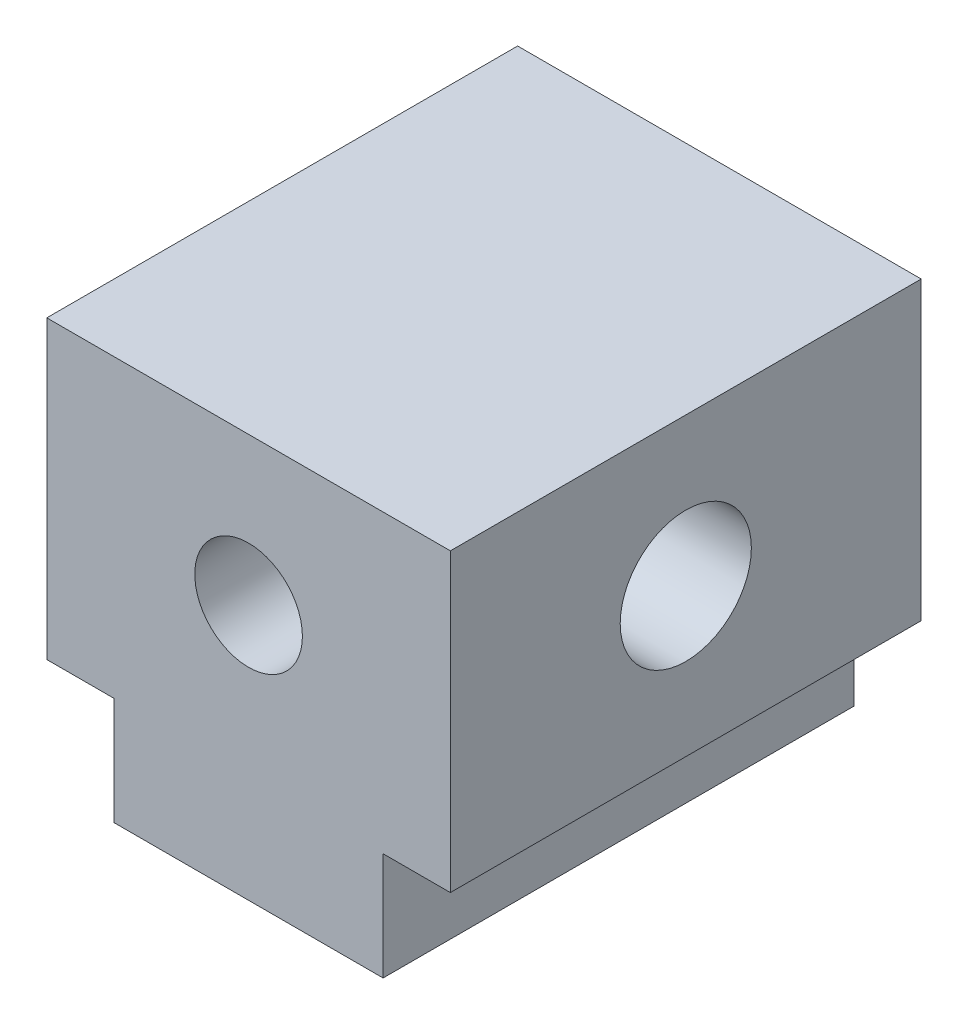
SolidWorks part; units mm, degrees
ref_plane "Front" through (0, 0, 0) normal (0, 0, 1) x (1, 0, 0)
ref_plane "Top" through (0, 0, 0) normal (0, 1, 0) x (1, 0, 0)
ref_plane "Right" through (0, 0, 0) normal (1, 0, 0) x (0, 0, -1)
sketch "Sketch1" plane through (0, 0, 0) normal (0, 1, 0) x (1, 0, 0)
  line L1 (-2, -3.5) -> (2, -3.5)
  line L2 (-2, -3.5) -> (-2, 3.5)
  line L3 (-2, 3.5) -> (2, 3.5)
  line L4 (2, -3.5) -> (2, 3.5)
  line L5 (-2, -3.5) -> (2, 3.5) construction
  line L6 (-2, 3.5) -> (2, -3.5) construction
  point P0 (0, 0)
  dimension "D1" = 4
  dimension "D2" = 7
extrude "Boss-Extrude1" add sketch "Sketch1" along normal blind 6
sketch "Sketch2" plane through (0, 0, 0) normal (0, -1, 0) x (1, 0, 0)
  line L1 (-0.75, -2.35) -> (0.75, -2.35)
  line L2 (-0.75, -2.35) -> (-0.75, 2.35)
  line L3 (-0.75, 2.35) -> (0.75, 2.35)
  line L4 (0.75, -2.35) -> (0.75, 2.35)
  line L5 (-0.75, -2.35) -> (0.75, 2.35) construction
  line L6 (-0.75, 2.35) -> (0.75, -2.35) construction
  point P0 (0, 0)
  dimension "D1" = 4.7
  dimension "D3" = 1.5
extrude "Cut-Extrude1" cut sketch "Sketch2" against normal blind 1.5
sketch "Sketch3" plane through (0, 0, 3.5) normal (0, 0, 1) x (1, 0, 0)
  line L0 (0, 1.5) -> (0, 3) construction
  line L1 (0, 3.8) -> (0, 3) construction
  line L4 (-0.75, 0) -> (0.75, 0)
  line L5 (0.75, 0) -> (0.75, 1.5)
  line L6 (0.75, 1.5) -> (-0.75, 1.5)
  line L7 (-0.75, 1.5) -> (-0.75, 0)
  line L8 (-0.75, 0) -> (0.75, 0) construction
  line L9 (0.75, 0) -> (0.75, 1.5) construction
  line L10 (0.75, 1.5) -> (-0.75, 1.5) construction
  line L11 (-0.75, 1.5) -> (-0.75, 0) construction
  circle A0 centre (0, 3.8) radius 0.8
  dimension "D3" = 1.6
  dimension "D2" = 1.5
  dimension "D1" = 0
extrude "Cut-Extrude2" cut sketch "Sketch3" against normal up to next
sketch "Sketch5" plane through (0, 0, 3.5) normal (0, 0, 1) x (1, 0, 0)
  line L1 (2, 6) -> (3, 6)
  line L2 (2, 6) -> (2, 1.6)
  line L3 (2, 1.6) -> (3, 1.6)
  line L4 (3, 6) -> (3, 1.6)
  line L5 (-3, 1.6) -> (3, 6) construction
  line L7 (-2, 6) -> (-3, 6)
  line L8 (-2, 6) -> (-2, 1.6)
  line L9 (-2, 1.6) -> (-3, 1.6)
  line L10 (-3, 6) -> (-3, 1.6)
  point P5 (0, 3.8)
  dimension "D1" = 6
extrude "Boss-Extrude2" add sketch "Sketch5" against normal up to surface (7 mm away) up to face at (0.8, 3.8, -3.5)
sketch "Sketch4" plane through (-3, 0, 0) normal (-1, 0, 0) x (0, 0, 1)
  line L0 (0, 6) -> (0, 3.8) construction
  line L1 (-3.5, 6) -> (3.5, 6) construction
  circle A0 centre (0, 3.8) radius 0.975
  dimension "D1" = 1.95
  dimension "D2" = 2.2
extrude "Cut-Extrude4" cut sketch "Sketch4" against normal through all
